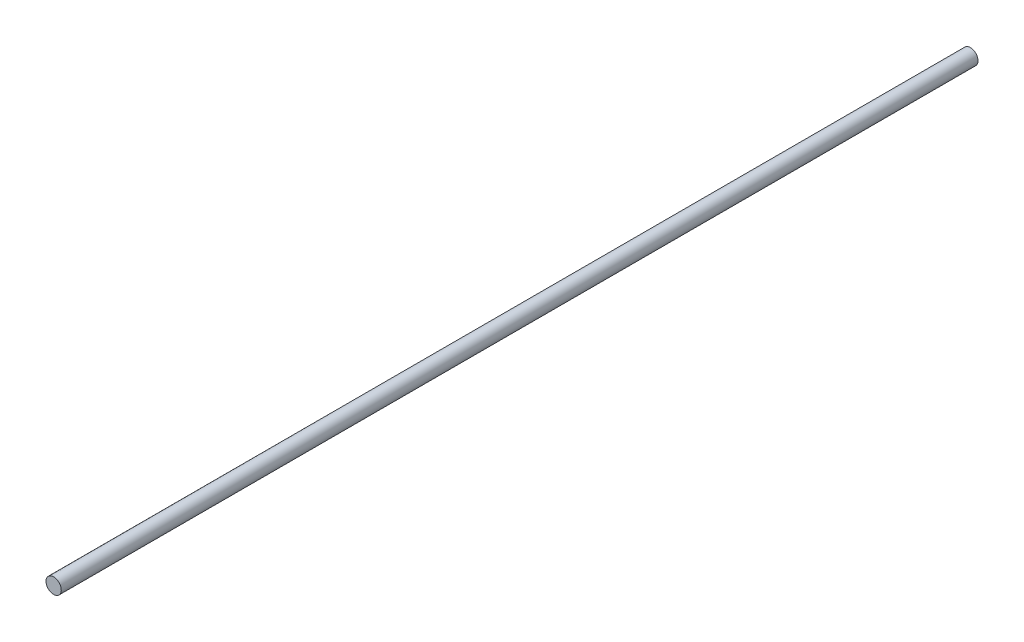
SolidWorks part; units mm, degrees
material "ﾊﾞﾙｻ"
ref_plane "正面" through (0, 0, 0) normal (0, 0, 1) x (1, 0, 0)
ref_plane "平面" through (0, 0, 0) normal (0, 1, 0) x (1, 0, 0)
ref_plane "右側面" through (0, 0, 0) normal (1, 0, 0) x (0, 0, -1)
sketch "ｽｹｯﾁ1" plane through (0, 0, 0) normal (0, 0, 1) x (1, 0, 0)
  circle A0 centre (0, 0) radius 1.25
  dimension "D1" = 2.5
extrude "ﾎﾞｽ - 押し出し1" add sketch "ｽｹｯﾁ1" along normal blind 150
